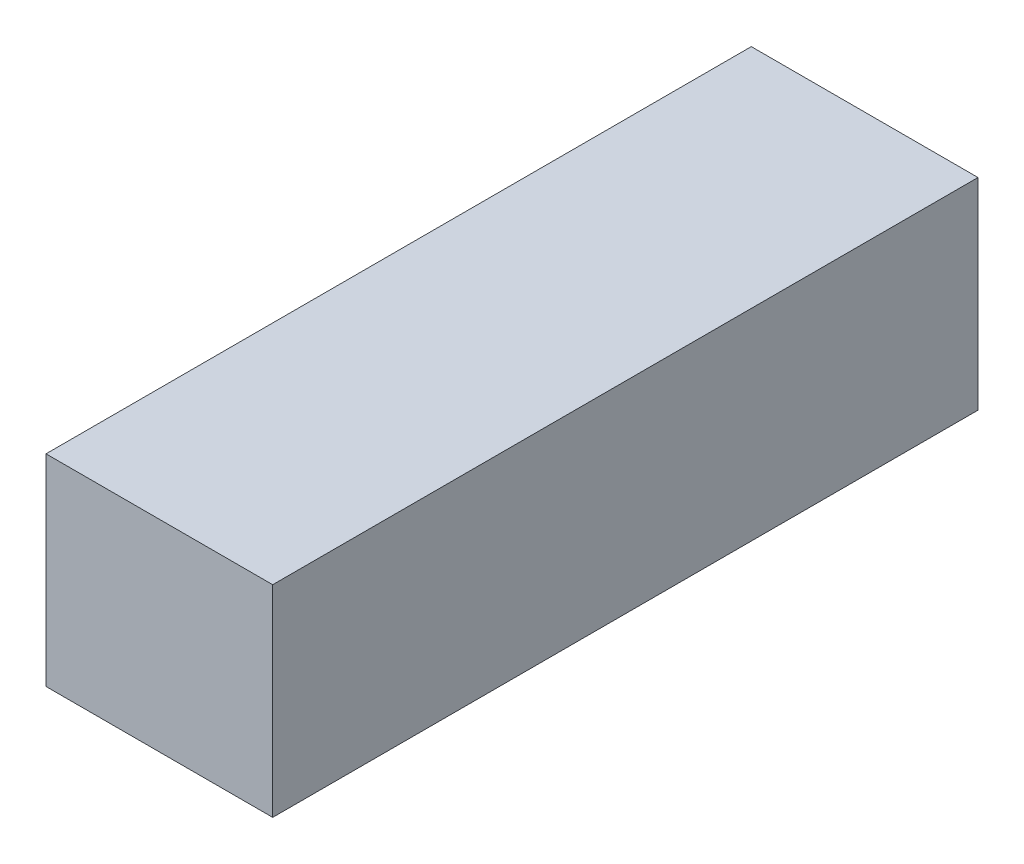
SolidWorks part; units mm, degrees
ref_plane "Front Plane" through (0, 0, 0) normal (0, 0, 1) x (1, 0, 0)
ref_plane "Top Plane" through (0, 0, 0) normal (0, 1, 0) x (1, 0, 0)
ref_plane "Right Plane" through (0, 0, 0) normal (1, 0, 0) x (0, 0, -1)
sketch "Sketch1" plane through (0, 0, 0) normal (0, 0, 1) x (1, 0, 0)
  line L1 (-2.25, 2) -> (2.25, 2)
  line L2 (-2.25, 2) -> (-2.25, -2)
  line L3 (-2.25, -2) -> (2.25, -2)
  line L4 (2.25, 2) -> (2.25, -2)
  line L5 (-2.25, 2) -> (2.25, -2) construction
  line L6 (-2.25, -2) -> (2.25, 2) construction
  point P0 (0, 0)
  dimension "D1" = 4.5
  dimension "D2" = 4
extrude "Boss-Extrude1" add sketch "Sketch1" along normal mid plane 14
